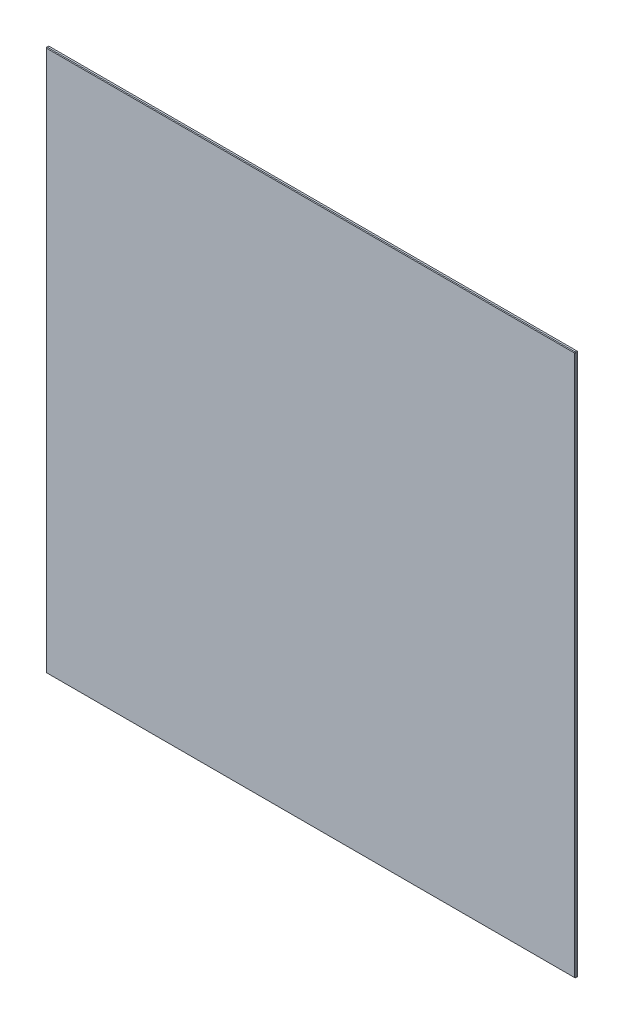
SolidWorks part; units mm, degrees
material "Glass"
ref_plane "Front Plane" through (0, 0, 0) normal (0, 0, 1) x (1, 0, 0)
ref_plane "Top Plane" through (0, 0, 0) normal (0, 1, 0) x (1, 0, 0)
ref_plane "Right Plane" through (0, 0, 0) normal (1, 0, 0) x (0, 0, -1)
sketch "Sketch1" plane through (0, 0, 0) normal (0, 0, 1) x (1, 0, 0)
  line L1 (-210, -215) -> (210, -215)
  line L2 (-210, -215) -> (-210, 215)
  line L3 (-210, 215) -> (210, 215)
  line L4 (210, -215) -> (210, 215)
  line L5 (-210, -215) -> (210, 215) construction
  line L6 (-210, 215) -> (210, -215) construction
  point P0 (0, 0)
  dimension "D1" = 420
  dimension "D2" = 430
extrude "Boss-Extrude1" add sketch "Sketch1" along normal blind 2.3813
chamfer "Chamfer1" distance 0.5 angle 45 12 edges at (0, 215, 0) (-210, 0, 0) (0, -215, 0) (210, 0, 0) (0, -215, 2.3813) (-210, 0, 2.3813) (0, 215, 2.3813) (210, 0, 2.3813) (210, -215, 1.1906) (210, 215, 1.1906) (-210, 215, 1.1906) (-210, -215, 1.1906)
